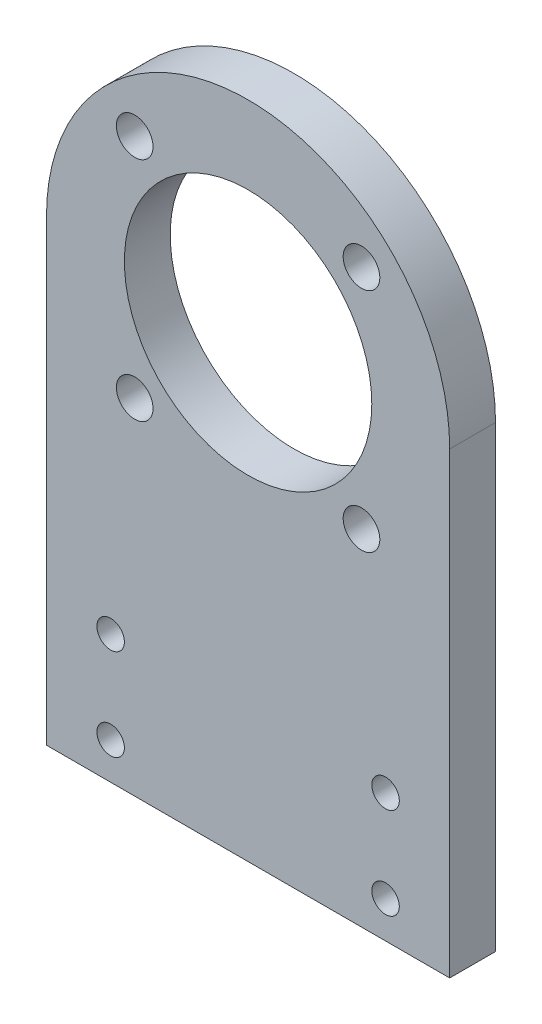
SolidWorks part; units mm, degrees
material "6063-O"
ref_plane "前视基准面" through (0, 0, 0) normal (0, 0, 1) x (1, 0, 0)
ref_plane "上视基准面" through (0, 0, 0) normal (0, 1, 0) x (1, 0, 0)
ref_plane "右视基准面" through (0, 0, 0) normal (1, 0, 0) x (0, 0, -1)
sketch "草图1" plane through (0, 0, 0) normal (0, 0, 1) x (1, 0, 0)
  line L0 (0, 148.1001) -> (0, -47.4393) construction
  line L1 (-22, 0) -> (22, 0)
  line L2 (-22, 0) -> (-22, 50)
  line L3 (-22, 50) -> (22, 50) construction
  line L4 (22, 0) -> (22, 50)
  line L5 (0, 50) -> (12.3744, 62.3744) construction
  arc A0 (22, 50) -> (-22, 50) centre (0, 50) ccw
  circle A1 centre (-15, 14) radius 1.5
  circle A2 centre (-15, 4) radius 1.5
  circle A3 centre (15, 4) radius 1.5
  circle A4 centre (15, 14) radius 1.5
  circle A5 centre (0, 50) radius 13.5
  circle A6 centre (0, 50) radius 17.5 construction
  circle A7 centre (12.3744, 62.3744) radius 2 construction
  circle A8 centre (12.3744, 37.6256) radius 2 construction
  circle A9 centre (-12.3744, 37.6256) radius 2 construction
  circle A10 centre (-12.3744, 62.3744) radius 2 construction
  point P5 (0, 0)
  point P30 (0, 50)
  dimension "D3" = 3
  dimension "D4" = 3
  dimension "D6" = 10
  dimension "D7" = 7
  dimension "D8" = 27
  dimension "D9" = 35
  dimension "D10" = 45
  dimension "D11" = 4
  dimension "D1" = 44
  dimension "D2" = 50
  dimension "D5" = 4
  dimension "D12" = 4
extrude "凸台-拉伸1" add sketch "草图1" along normal blind 5
sketch "草图2" plane through (0, 0, 0) normal (0, 0, -1) x (-1, 0, 0)
  line L0 (0, 50) -> (32.4134, 50) construction
  line L1 (0, 50) -> (29.0311, 79.0311) construction
  circle A1 centre (0, 50) radius 14.5 construction
  circle A2 centre (0, 50) radius 17.5 construction
  circle A3 centre (12.3744, 62.3744) radius 2
  circle A4 centre (12.3744, 37.6256) radius 2
  circle A5 centre (-12.3744, 37.6256) radius 2
  circle A6 centre (-12.3744, 62.3744) radius 2
  circle A7 centre (0, 50) radius 13.5 construction
  point P18 (0, 50)
  dimension "D2" = 4
  dimension "D5" = 35
  dimension "D3" = 45
  dimension "D1" = 3
  dimension "D4" = 4
extrude "切除-拉伸1" cut sketch "草图2" against normal through all
